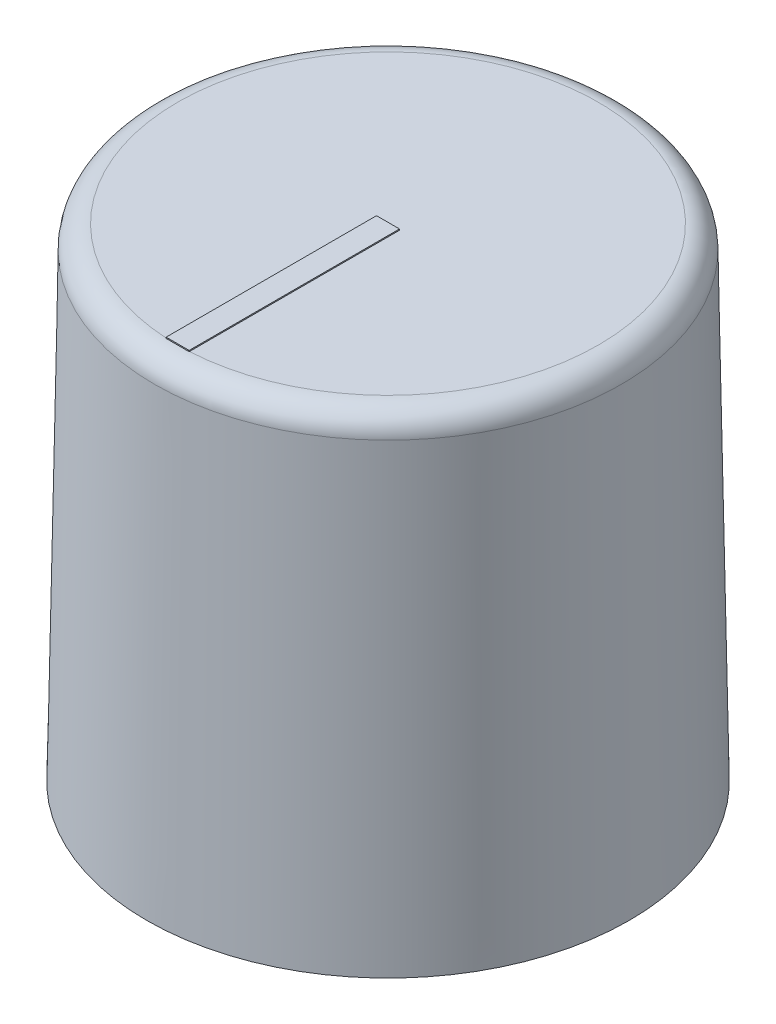
SolidWorks part; units mm, degrees
ref_plane "Front Plane" through (0, 0, 0) normal (0, 0, 1) x (1, 0, 0)
ref_plane "Top Plane" through (0, 0, 0) normal (0, 1, 0) x (1, 0, 0)
ref_plane "Right Plane" through (0, 0, 0) normal (1, 0, 0) x (0, 0, -1)
sketch "Sketch1" plane through (0, 0, 0) normal (0, 1, 0) x (1, 0, 0)
  circle A0 centre (0, 0) radius 10.5
  dimension "D1" = 21
extrude "Boss-Extrude1" add sketch "Sketch1" along normal blind 21 draft 1
sketch "Sketch2" plane through (0, 0, 0) normal (0, -1, 0) x (1, 0, 0)
  circle A0 centre (0, 0) radius 9
  dimension "D1" = 18
extrude "Cut-Extrude1" cut sketch "Sketch2" against normal offset from surface (20 mm away) 1 up to face at (0, 21, 10.1334)
fillet "Fillet1" radius 1 1 edges at (0, 21, 10.1334)
sketch "Sketch3" plane through (0, 21, 0) normal (0, 1, 0) x (1, 0, 0)
  line L1 (-0.5, -9.1507) -> (0.5, -9.1507)
  line L2 (-0.5, -9.1507) -> (-0.5, 0)
  line L3 (-0.5, 0) -> (0.5, 0)
  line L4 (0.5, -9.1507) -> (0.5, 0)
  point P4 (0, 0)
  point P5 (0, -9.1507)
  dimension "D1" = 1
extrude "Boss-Extrude2" add sketch "Sketch3" along normal blind 0.05
